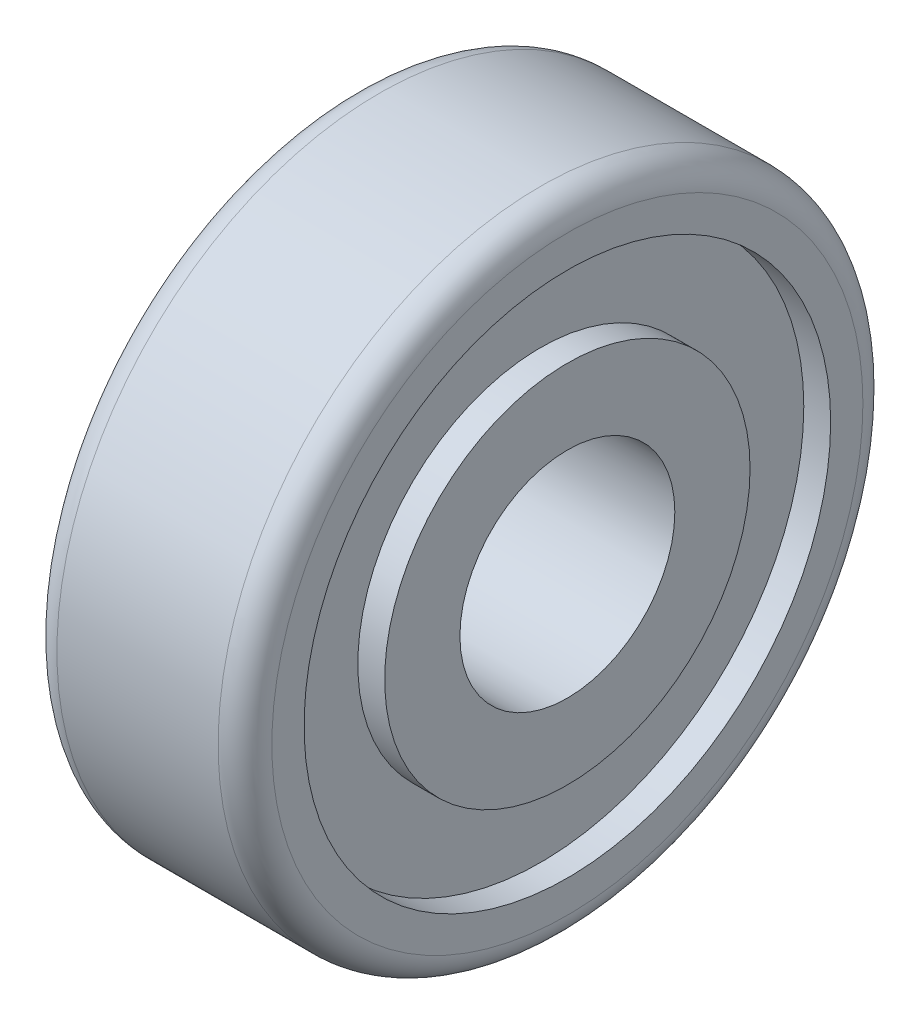
SolidWorks part; units mm, degrees
ref_plane "Front Plane" through (0, 0, 0) normal (0, 0, 1) x (1, 0, 0)
ref_plane "Top Plane" through (0, 0, 0) normal (0, 1, 0) x (1, 0, 0)
ref_plane "Right Plane" through (0, 0, 0) normal (1, 0, 0) x (0, 0, -1)
sketch "Sketch1" plane through (0, 0, 0) normal (1, 0, 0) x (0, 0, -1)
  circle A0 centre (0, 0) radius 6
  circle A1 centre (0, 0) radius 2
  dimension "D1" = 12
  dimension "D2" = 4
extrude "Boss-Extrude1" add sketch "Sketch1" along normal blind 4
fillet "Fillet1" radius 0.5 2 edges at (0, 0, -6) (4, 0, -6)
sketch "Sketch2" plane through (4, 0, 0) normal (1, 0, 0) x (0, 0, -1)
  circle A0 centre (0, 0) radius 3.4
  circle A1 centre (0, 0) radius 4.9
  dimension "D1" = 6.8
  dimension "D2" = 9.8
extrude "Cut-Extrude1" cut sketch "Sketch2" against normal blind 0.5
sketch "Sketch3" plane through (0, 0, 0) normal (-1, 0, 0) x (0, 0, 1)
  circle A1 centre (0, 0) radius 4.9
  circle A2 centre (0, 0) radius 4.9
  circle A3 centre (0, 0) radius 3.4
  circle A4 centre (0, 0) radius 3.4
  dimension "D1" = 0
  dimension "D2" = 0
extrude "Cut-Extrude2" cut sketch "Sketch3" against normal blind 0.5
